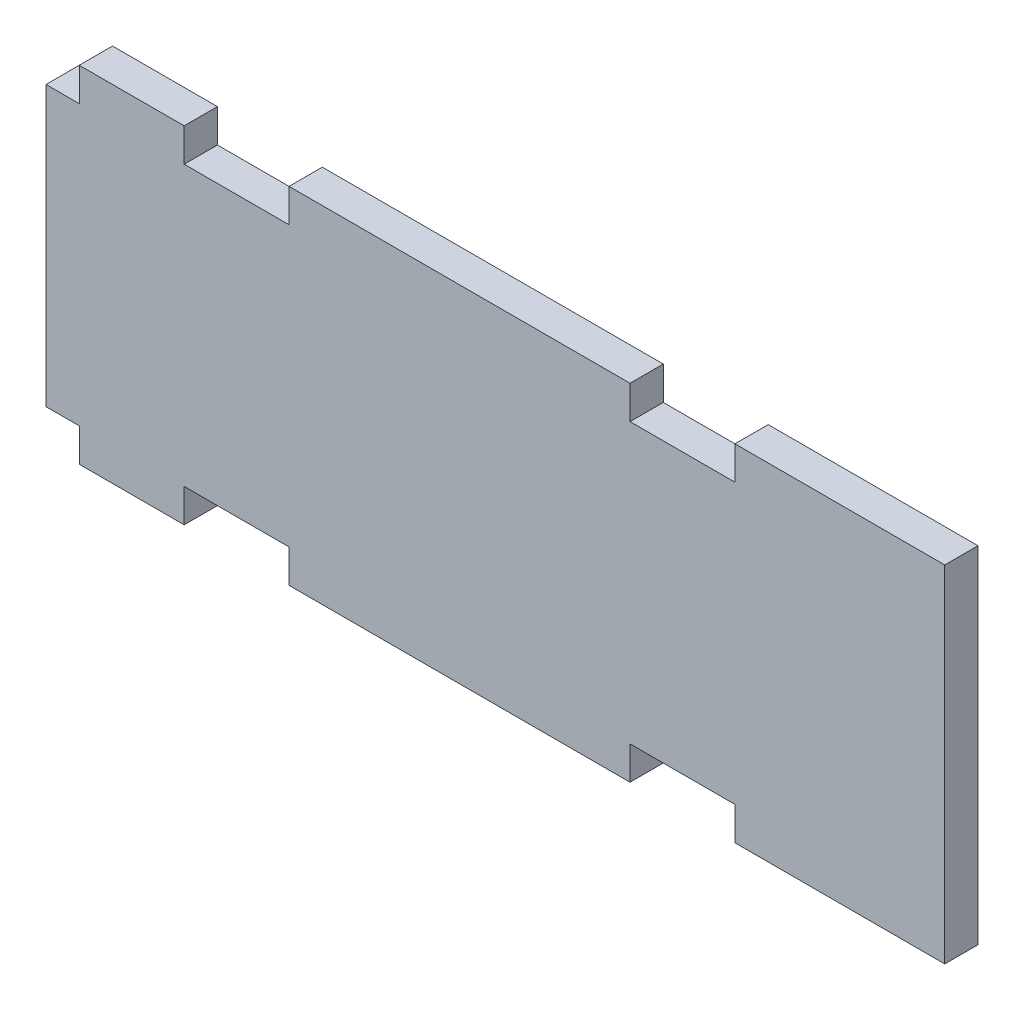
SolidWorks part; units mm, degrees
ref_plane "XY PLANE" through (0, 0, 0) normal (0, 0, 1) x (1, 0, 0)
ref_plane "XZ PLANE" through (0, 0, 0) normal (0, 1, 0) x (1, 0, 0)
ref_plane "YZ PLANE" through (0, 0, 0) normal (1, 0, 0) x (0, 0, -1)
sketch "Sketch1" plane through (0, 0, 0) normal (0, 0, 1) x (1, 0, 0)
  line L0 (55.67, 0) -> (65.67, 0)
  line L1 (0, -32.94) -> (85.67, -32.94)
  line L2 (0, -32.94) -> (0, 0)
  line L3 (0, 0) -> (85.67, 0)
  line L4 (85.67, -32.94) -> (85.67, 0)
  line L5 (13.17, -29.77) -> (23.17, -29.77)
  line L6 (13.17, -29.77) -> (13.17, -32.94)
  line L7 (13.17, -32.94) -> (23.17, -32.94)
  line L8 (23.17, -29.77) -> (23.17, -32.94)
  line L9 (13.17, 0) -> (23.17, 0)
  line L10 (13.17, 0) -> (13.17, -3.17)
  line L11 (13.17, -3.17) -> (23.17, -3.17)
  line L12 (23.17, 0) -> (23.17, -3.17)
  line L13 (55.67, 0) -> (55.67, -3.17)
  line L14 (55.67, -3.17) -> (65.67, -3.17)
  line L15 (65.67, 0) -> (65.67, -3.17)
  line L16 (55.67, -29.77) -> (65.67, -29.77)
  line L17 (55.67, -29.77) -> (55.67, -32.94)
  line L18 (55.67, -32.94) -> (65.67, -32.94)
  line L19 (65.67, -29.77) -> (65.67, -32.94)
  line L32 (0, 0) -> (3.17, 0)
  line L33 (0, 0) -> (0, -3.17)
  line L34 (0, -3.17) -> (3.17, -3.17)
  line L35 (3.17, 0) -> (3.17, -3.17)
  line L36 (0, -32.94) -> (3.17, -32.94)
  line L37 (0, -32.94) -> (0, -29.77)
  line L38 (0, -29.77) -> (3.17, -29.77)
  line L39 (3.17, -32.94) -> (3.17, -29.77)
  point P20 (0, 0)
  point P21 (0, 0)
  point P22 (0, 0)
  dimension "D1" = 3.17
  dimension "D2" = 10
  dimension "D3" = 10
  dimension "D4" = 3.17
  dimension "D5" = 20
  dimension "D6" = 10
  dimension "D7" = 85.67
  dimension "D8" = 32.94
extrude "Boss-Extrude1" add sketch "Sketch1" along normal blind 3.17 contours L39 L1 L6 L5 L8 L17 L16 L19 L4 L3 L15 L14 L13 L12 L11 L10 L35 L34 L2 L38
